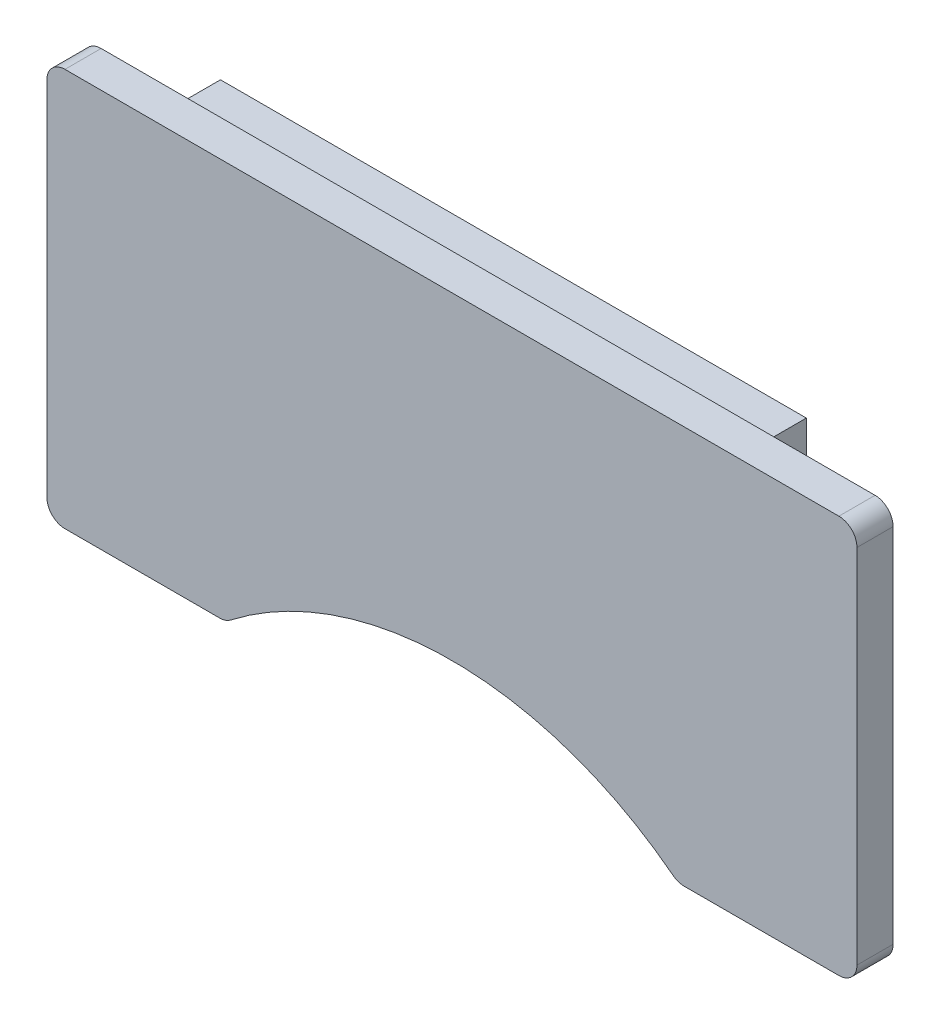
SolidWorks part; units mm, degrees
ref_plane "Front Plane" through (0, 0, 0) normal (0, 0, 1) x (1, 0, 0)
ref_plane "Top Plane" through (0, 0, 0) normal (0, 1, 0) x (1, 0, 0)
ref_plane "Right Plane" through (0, 0, 0) normal (1, 0, 0) x (0, 0, -1)
sketch "Sketch1" plane through (0, 0, 0) normal (0, 0, 1) x (1, 0, 0)
  line L1 (-28.448, -13.97) -> (28.448, -13.97)
  line L2 (-28.448, -13.97) -> (-28.448, 13.97)
  line L3 (-28.448, 13.97) -> (28.448, 13.97)
  line L4 (28.448, -13.97) -> (28.448, 13.97)
  line L5 (-28.448, -13.97) -> (28.448, 13.97) construction
  line L6 (-28.448, 13.97) -> (28.448, -13.97) construction
  point P0 (0, 0)
  dimension "D1" = 27.94
  dimension "D2" = 56.896
extrude "Boss-Extrude1" add sketch "Sketch1" along normal blind 2.54
sketch "Sketch2" plane through (0, 0, 2.54) normal (0, 0, 1) x (1, 0, 0)
  line L0 (-28.448, -13.97) -> (28.448, -13.97) construction
  line L1 (-15.875, -13.97) -> (15.875, -13.97)
  arc A0 (-15.875, -13.97) -> (15.875, -13.97) centre (0, -33.7979) cw
  point P3 (0, -8.3979)
  dimension "D1" = 25.4
  dimension "D2" = 31.75
extrude "Cut-Extrude1" cut sketch "Sketch2" against normal through all
fillet "Fillet1" radius 1.27 6 edges at (-28.448, -13.97, 1.27) (28.448, -13.97, 1.27) (28.448, 13.97, 1.27) (-28.448, 13.97, 1.27) (-15.875, -13.97, 1.27) (15.875, -13.97, 1.27)
sketch "Sketch4" plane through (0, 0, 0) normal (1, 0, 0) x (0, 0, -1)
  line L0 (0, 6.604) -> (9.652, 6.604)
  line L1 (0, -12.7) -> (0, 12.7) construction
  line L2 (9.652, 6.604) -> (9.652, -6.604)
  line L3 (9.652, -6.604) -> (0, -6.604)
  line L4 (0, -6.604) -> (0, -4.064)
  line L5 (0, -4.064) -> (7.112, -4.064)
  line L6 (7.112, -4.064) -> (7.112, 4.064)
  line L7 (7.112, 4.064) -> (0, 4.064)
  line L8 (0, 4.064) -> (0, 6.604)
  line L9 (0, 6.604) -> (0, 4.064)
  line L10 (0, -4.064) -> (0, -6.604)
  point P6 (3.556, 4.064)
  point P11 (7.112, 0)
  dimension "D1" = 2.54
  dimension "D2" = 2.54
  dimension "D3" = 2.54
  dimension "D4" = 7.112
  dimension "D5" = 8.128
extrude "Extrude-Thin1" add sketch "Sketch4" against normal up to surface (28.448 mm away) and the other way blind 12.7 thin contours L5 L6 L7
